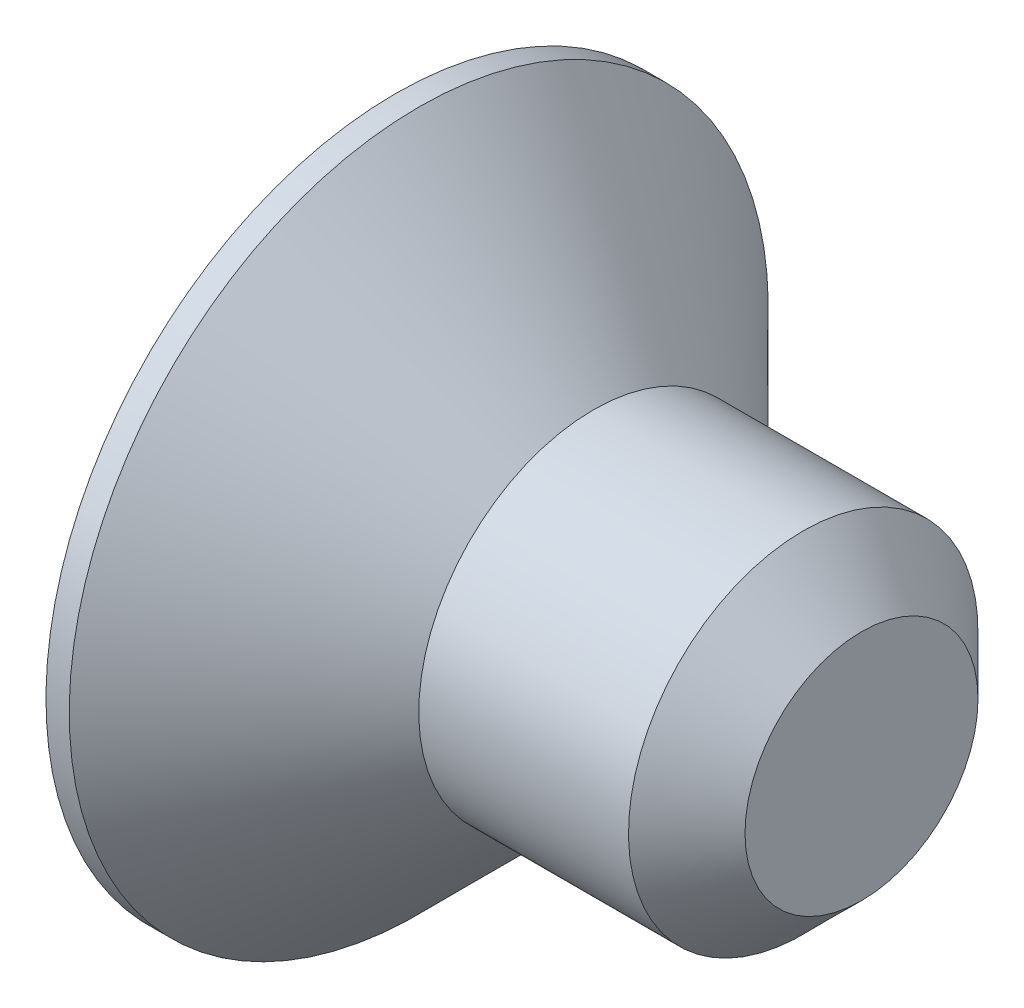
SolidWorks part; units mm, degrees
ref_plane "Plan de face" through (0, 0, 0) normal (0, 0, 1) x (1, 0, 0)
ref_plane "Plan de dessus" through (0, 0, 0) normal (0, 1, 0) x (1, 0, 0)
ref_plane "Plan de droite" through (0, 0, 0) normal (1, 0, 0) x (0, 0, -1)
sketch "Esquisse1" plane through (0, 0, 0) normal (0, 0, 1) x (1, 0, 0)
  line L0 (0, 0) -> (0, 3)
  line L1 (0, 3) -> (0.2, 3)
  line L2 (0.2, 3) -> (1.7, 1.5)
  line L3 (1.7, 1.5) -> (4, 1.5)
  line L4 (4, 1.5) -> (4, 0)
  line L5 (4, 0) -> (0, 0) construction
  line L6 (0, 0) -> (4, 0)
  dimension "D1" = 1.7
  dimension "D2" = 4
  dimension "D3" = 3
  dimension "D4" = 6
  dimension "D5" = 45
revolve "Révolution1" add sketch "Esquisse1" angle 360 about L5
chamfer "Chanfrein1" distance 0.5 angle 45 1 edges at (4, 1.5, 0)
sketch "Esquisse2" plane through (0, 0, 0) normal (-1, 0, 0) x (0, 0, 1)
  line L1 (0, 1.1547) -> (-1, 0.5774)
  line L2 (-1, 0.5774) -> (-1, -0.5774)
  line L3 (-1, -0.5774) -> (0, -1.1547)
  line L4 (0, -1.1547) -> (1, -0.5774)
  line L5 (1, -0.5774) -> (1, 0.5774)
  line L6 (1, 0.5774) -> (0, 1.1547)
  circle A0 centre (0, 0) radius 1 construction
  dimension "D1" = 2
extrude "Enlèv. mat.-Extru.1" cut sketch "Esquisse2" against normal blind 1.2
